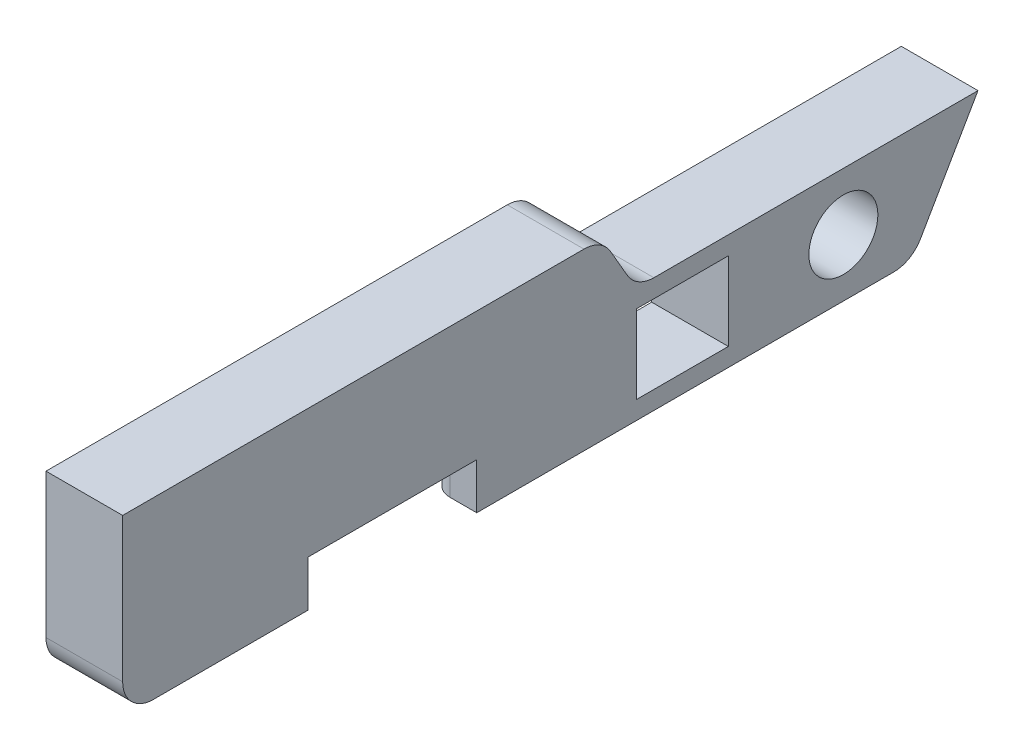
SolidWorks part; units mm, degrees
ref_plane "Front Plane" through (0, 0, 0) normal (0, 0, 1) x (1, 0, 0)
ref_plane "Top Plane" through (0, 0, 0) normal (0, 1, 0) x (1, 0, 0)
ref_plane "Right Plane" through (0, 0, 0) normal (1, 0, 0) x (0, 0, -1)
sketch "Sketch1" plane through (0, 0, 0) normal (1, 0, 0) x (0, 0, -1)
  line L0 (0, 2.54) -> (0, 14.4743)
  line L1 (0, 14.4743) -> (38.2059, 14.4743)
  line L2 (40.4056, 13.2043) -> (41.7967, 10.795)
  line L3 (43.9964, 9.525) -> (70.8408, 9.525)
  line L4 (70.8408, 9.525) -> (66.0747, 1.27)
  line L5 (63.875, 0) -> (2.54, 0)
  line L6 (38.7559, 14.4743) -> (0, 14.4743) construction
  line L7 (44.033, 9.525) -> (70.4215, 9.525) construction
  line L8 (70.4215, 8.7988) -> (65.8181, 0.8255) construction
  line L9 (40.1307, 13.6806) -> (41.7783, 10.8267) construction
  arc A0 (0, 2.54) -> (2.54, 0) centre (2.54, 2.54) ccw
  arc A1 (66.0747, 1.27) -> (63.875, 0) centre (63.875, 2.54) cw
  arc A2 (41.7967, 10.795) -> (43.9964, 9.525) centre (43.9964, 12.065) ccw
  arc A3 (38.2059, 14.4743) -> (40.4056, 13.2043) centre (38.2059, 11.9343) cw
  point P17 (0, 0)
  dimension "D1" = 2.54
extrude "Boss-Extrude1" add sketch "Sketch1" along normal blind 6.35
sketch "Sketch2" plane through (6.35, 0, 0) normal (1, 0, 0) x (0, 0, -1)
  line L0 (2.54, 0) -> (63.875, 0) construction
  line L1 (42.545, 8.0137) -> (50.165, 8.0137)
  line L2 (42.545, 8.0137) -> (42.545, 1.5113)
  line L3 (42.545, 1.5113) -> (50.165, 1.5113)
  line L4 (50.165, 8.0137) -> (50.165, 1.5113)
  line L5 (15.3543, 0) -> (29.3243, 0)
  line L6 (15.3543, 0) -> (15.3543, 3.81)
  line L7 (15.3543, 3.81) -> (29.3243, 3.81)
  line L8 (29.3243, 0) -> (29.3243, 3.81)
  line L9 (22.3393, 3.81) -> (22.3393, 0) construction
  line L11 (-0.3683, 1.651) -> (-0.3683, 47.625) construction
  line L12 (42.545, 8.0137) -> (50.165, 1.5113) construction
  line L13 (52.5777, 9.525) -> (52.5777, 0) construction
  line L14 (70.8408, 9.525) -> (43.9964, 9.525) construction
  line L15 (0, 14.4743) -> (0, 2.54) construction
  circle A0 centre (59.69, 4.7625) radius 2.8575
  point P15 (46.355, 4.7625)
  point P22 (52.5777, 4.7625)
  dimension "D4" = 5.715
  dimension "D1" = 3.81
  dimension "D2" = 22.7076
  dimension "D3" = 13.97
  dimension "D5" = 6.5024
  dimension "D6" = 7.62
  dimension "D7" = 59.69
  dimension "D8" = 13.335
extrude "Cut-Extrude1" cut sketch "Sketch2" against normal through all
sketch "Sketch3" plane through (0, 0, -29.3243) normal (0, 0, 1) x (1, 0, 0)
  line L1 (6.35, 14.4743) -> (6.35, 2.54) construction
  line L2 (0, 3.81) -> (5.334, 3.81)
  line L4 (0, 3.81) -> (0, 8.89)
  line L5 (0, 8.89) -> (5.334, 8.89)
  line L6 (5.334, 3.81) -> (5.334, 8.89)
  line L7 (0, 3.81) -> (6.35, 3.81) construction
  line L8 (0, 14.4743) -> (0, 2.54) construction
  dimension "D1" = 1.016
  dimension "D2" = 5.08
extrude "Cut-Extrude2" cut sketch "Sketch3" along normal up to surface (13.97 mm away) up to face at (3.175, 1.905, -15.3543)
sketch "Sketch4" plane through (0, 0, 0) normal (1, 0, 0) x (0, 0, -1)
  line L0 (29.3243, 0) -> (63.875, 0) construction
  line L1 (9.0043, 11.6817) -> (33.1343, 11.6817)
  line L2 (9.0043, 11.6817) -> (9.0043, 0)
  line L3 (9.0043, 0) -> (33.1343, 0)
  line L4 (33.1343, 11.6817) -> (33.1343, 0)
  line L5 (15.3543, 3.81) -> (15.3543, 0) construction
  dimension "D1" = 24.13
  dimension "D2" = 6.35
extrude "Cut-Extrude3" cut sketch "Sketch4" along normal blind 2.54
sketch "Sketch5" plane through (0, 0, 0) normal (-1, 0, 0) x (0, 0, 1)
  line L1 (-29.3751, 3.81) -> (-15.4051, 3.81)
  line L2 (-29.3751, 3.81) -> (-29.3751, 0)
  line L3 (-29.3751, 0) -> (-15.4051, 0)
  line L4 (-15.4051, 3.81) -> (-15.4051, 0)
extrude "Boss-Extrude2" [suppressed] add sketch "Sketch5" against normal through all
fillet "Fillet1" radius 1.5875 6 edges at (0, 5.8408, -9.0043) (0, 11.6817, -21.0693) (0, 5.8408, -33.1343) (2.54, 4.445, -29.3243) (2.54, 4.445, -15.3543) (2.54, 8.89, -22.3393)
mirror "Mirror1" [suppressed] about plane through (0, 0, 0) normal (1, 0, 0)
